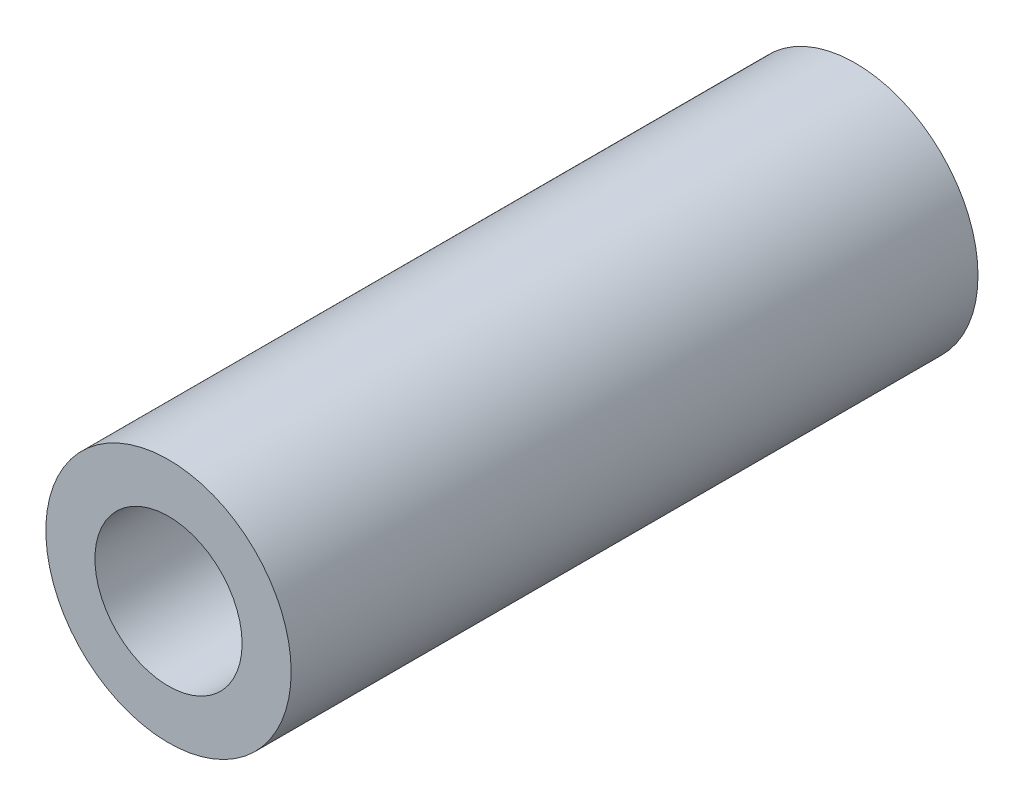
SolidWorks part; units mm, degrees
material "ﾎﾟﾘｵｷｼﾒﾁﾚﾝ(POM)ｱｾﾀｰﾙ共重合体"
ref_plane "Front Plane" through (0, 0, 0) normal (0, 0, 1) x (1, 0, 0)
ref_plane "Top Plane" through (0, 0, 0) normal (0, 1, 0) x (1, 0, 0)
ref_plane "Right Plane" through (0, 0, 0) normal (1, 0, 0) x (0, 0, -1)
sketch "Sketch2" plane through (0, 0, 0) normal (0, 0, 1) x (1, 0, 0)
  circle A0 centre (0, 0) radius 2.5
  circle A1 centre (0, 0) radius 1.5
  dimension "D1" = 3
  dimension "D2" = 5
  dimension "D3" = 5
extrude "Boss-Extrude1" add sketch "Sketch2" along normal blind 14
